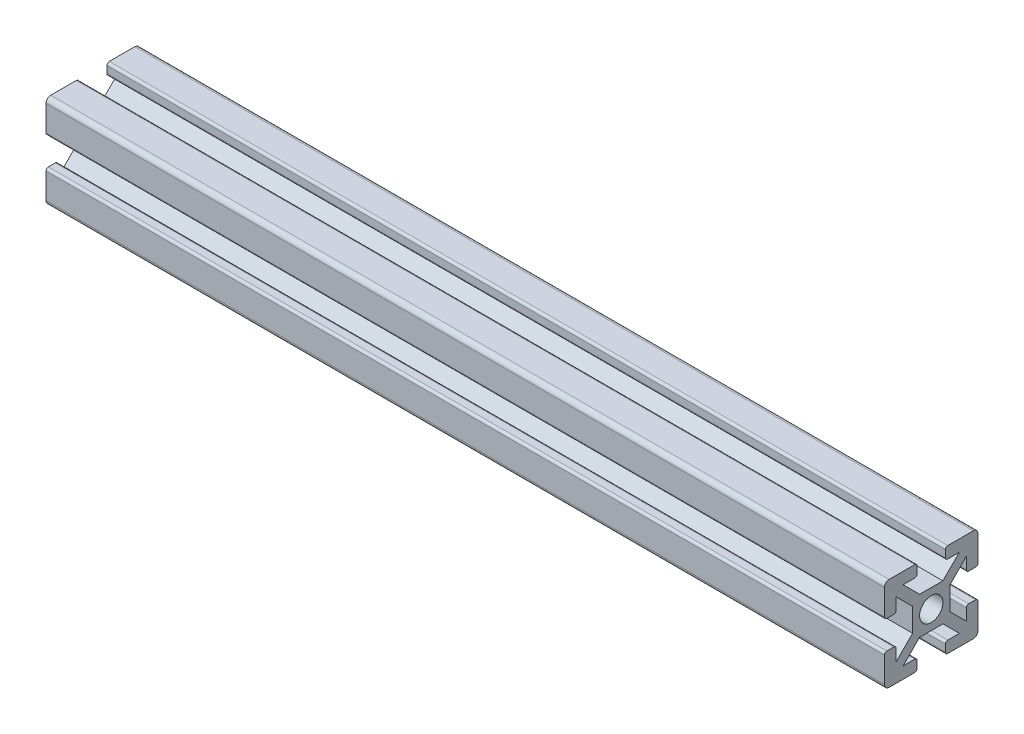
SolidWorks part; units mm, degrees
ref_plane "Front Plane" through (0, 0, 0) normal (0, 0, 1) x (1, 0, 0)
ref_plane "Top Plane" through (0, 0, 0) normal (0, 1, 0) x (1, 0, 0)
ref_plane "Right Plane" through (0, 0, 0) normal (1, 0, 0) x (0, 0, -1)
sketch "Sketch1" plane through (0, 0, 0) normal (0, 0, 1) x (1, 0, 0)
  line L0 (-81.5934, 0) -> (98.4066, 0)
  dimension "D1" = 180
other "Aluminium prof ALUMINIUM PROF(1)"
ref_plane "Plane1" through (-81.5934, 0, 0) normal (1, 0, 0) x (0, 1, 0)
sketch "Sketch11" plane through (-81.5934, 0, 0) normal (1, 0, 0) x (0, 1, 0)
  line L0 (0, 0) -> (0, 19.0058) construction
  line L9 (0, 0) -> (23.0409, 0) construction
  line L10 (23.0409, 0) -> (23.0409, -0.0585) construction
  line L11 (23.0409, -0.0585) -> (23.0409, 0) construction
  line L13 (-2.5, 4) -> (2.5, 4)
  line L14 (2.5, 4) -> (6.0355, 7.5355)
  line L15 (6.0355, 7.5355) -> (3.5355, 7.5355)
  line L16 (3.0355, 8.0355) -> (3.0355, 9.5355)
  line L17 (3.5355, 10.0355) -> (9.0355, 10.0355)
  line L18 (10.0355, 9.0355) -> (10.0355, 3.5355)
  line L19 (9.5355, 3.0355) -> (8.0355, 3.0355)
  line L20 (7.5355, 3.5355) -> (7.5355, 6.0355)
  line L21 (7.5355, 6.0355) -> (4, 2.5)
  line L22 (4, 2.5) -> (4, -2.5)
  line L23 (-10.0355, 9.0355) -> (-10.0355, 3.5355)
  line L24 (-4, 2.5) -> (-4, -2.5)
  line L25 (-7.5355, 6.0355) -> (-4, 2.5)
  line L26 (-7.5355, 3.5355) -> (-7.5355, 6.0355)
  line L27 (-9.5355, 3.0355) -> (-8.0355, 3.0355)
  line L28 (-3.5355, 10.0355) -> (-9.0355, 10.0355)
  line L29 (-3.0355, 8.0355) -> (-3.0355, 9.5355)
  line L30 (-6.0355, 7.5355) -> (-3.5355, 7.5355)
  line L31 (-2.5, 4) -> (-6.0355, 7.5355)
  line L32 (3.5355, -10.0355) -> (9.0355, -10.0355)
  line L33 (-2.5, -4) -> (-6.0355, -7.5355)
  line L34 (-6.0355, -7.5355) -> (-3.5355, -7.5355)
  line L35 (-3.0355, -8.0355) -> (-3.0355, -9.5355)
  line L36 (-3.5355, -10.0355) -> (-9.0355, -10.0355)
  line L37 (-9.5355, -3.0355) -> (-8.0355, -3.0355)
  line L38 (-7.5355, -3.5355) -> (-7.5355, -6.0355)
  line L39 (-7.5355, -6.0355) -> (-4, -2.5)
  line L40 (-10.0355, -9.0355) -> (-10.0355, -3.5355)
  line L41 (7.5355, -6.0355) -> (4, -2.5)
  line L42 (7.5355, -3.5355) -> (7.5355, -6.0355)
  line L43 (9.5355, -3.0355) -> (8.0355, -3.0355)
  line L44 (10.0355, -9.0355) -> (10.0355, -3.5355)
  line L45 (3.0355, -8.0355) -> (3.0355, -9.5355)
  line L46 (6.0355, -7.5355) -> (3.5355, -7.5355)
  line L47 (2.5, -4) -> (6.0355, -7.5355)
  line L48 (-2.5, -4) -> (2.5, -4)
  circle A0 centre (0, 0) radius 2.5
  arc A1 (-10.0355, 9.0355) -> (-9.0355, 10.0355) centre (-9.0355, 9.0355) cw
  arc A2 (-9.0355, -10.0355) -> (-10.0355, -9.0355) centre (-9.0355, -9.0355) cw
  arc A3 (9.0355, -10.0355) -> (10.0355, -9.0355) centre (9.0355, -9.0355) ccw
  arc A4 (9.0355, 10.0355) -> (10.0355, 9.0355) centre (9.0355, 9.0355) cw
  arc A5 (-9.5355, -3.0355) -> (-10.0355, -3.5355) centre (-9.5355, -3.5355) ccw
  arc A6 (-8.0355, -3.0355) -> (-7.5355, -3.5355) centre (-8.0355, -3.5355) cw
  arc A7 (-3.5355, -7.5355) -> (-3.0355, -8.0355) centre (-3.5355, -8.0355) cw
  arc A8 (-3.0355, -9.5355) -> (-3.5355, -10.0355) centre (-3.5355, -9.5355) cw
  arc A9 (3.5355, -10.0355) -> (3.0355, -9.5355) centre (3.5355, -9.5355) cw
  arc A10 (3.0355, -8.0355) -> (3.5355, -7.5355) centre (3.5355, -8.0355) cw
  arc A11 (9.5355, -3.0355) -> (10.0355, -3.5355) centre (9.5355, -3.5355) cw
  arc A12 (7.5355, -3.5355) -> (8.0355, -3.0355) centre (8.0355, -3.5355) cw
  arc A13 (10.0355, 3.5355) -> (9.5355, 3.0355) centre (9.5355, 3.5355) cw
  arc A14 (8.0355, 3.0355) -> (7.5355, 3.5355) centre (8.0355, 3.5355) cw
  arc A15 (3.5355, 7.5355) -> (3.0355, 8.0355) centre (3.5355, 8.0355) cw
  arc A16 (3.0355, 9.5355) -> (3.5355, 10.0355) centre (3.5355, 9.5355) cw
  arc A17 (-3.5355, 10.0355) -> (-3.0355, 9.5355) centre (-3.5355, 9.5355) cw
  arc A18 (-3.0355, 8.0355) -> (-3.5355, 7.5355) centre (-3.5355, 8.0355) cw
  arc A19 (-7.5355, 3.5355) -> (-8.0355, 3.0355) centre (-8.0355, 3.5355) cw
  arc A20 (-10.0355, 3.5355) -> (-9.5355, 3.0355) centre (-9.5355, 3.5355) ccw
  point P26 (0, 4)
  point P29 (-4, 0)
  point P30 (4, 0)
  point P44 (0, -4)
  point P48 (-10.0355, 10.0355)
  point P51 (-10.0355, -10.0355)
  point P54 (10.0355, -10.0355)
  point P57 (10.0355, 10.0355)
  point P60 (-10.0355, -3.0355)
  point P63 (-7.5355, -3.0355)
  point P66 (-3.0355, -7.5355)
  point P69 (-3.0355, -10.0355)
  point P72 (3.0355, -10.0355)
  point P75 (3.0355, -7.5355)
  point P78 (10.0355, -3.0355)
  point P81 (7.5355, -3.0355)
  point P84 (10.0355, 3.0355)
  point P87 (7.5355, 3.0355)
  point P90 (3.0355, 7.5355)
  point P93 (3.0355, 10.0355)
  point P96 (-3.0355, 10.0355)
  point P99 (-3.0355, 7.5355)
  point P102 (-7.5355, 3.0355)
  point P105 (-10.0355, 3.0355)
  point P106 (0, 0)
  dimension "D5" = 4
  dimension "D12" = 1
  dimension "D13" = 0.5
  dimension "D1" = 135
  dimension "D2" = 2.5
  dimension "D3" = 4
  dimension "D4" = 2.5
  dimension "D6" = 7
  dimension "D7" = 7
  dimension "D8" = 3
  dimension "D9" = 3
  dimension "D10" = 5
  dimension "D11" = 23.0409
